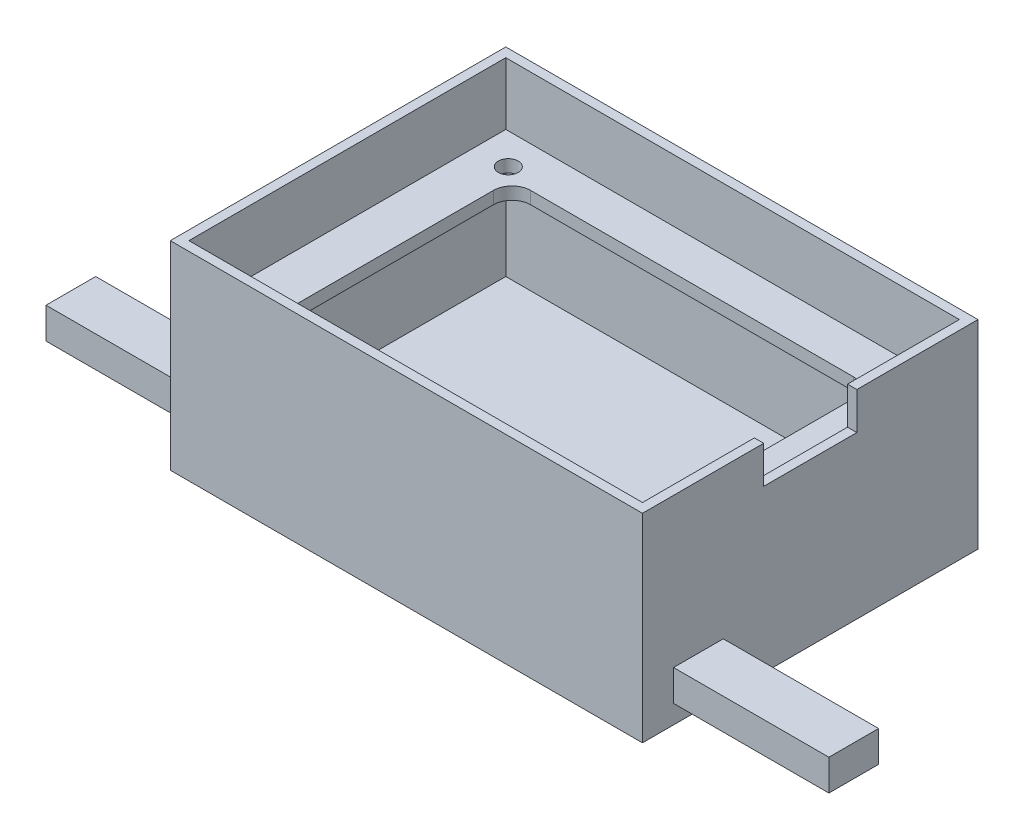
SolidWorks part; units mm, degrees
ref_plane "Front Plane" through (0, 0, 0) normal (0, 0, 1) x (1, 0, 0)
ref_plane "Top Plane" through (0, 0, 0) normal (0, 1, 0) x (1, 0, 0)
ref_plane "Right Plane" through (0, 0, 0) normal (1, 0, 0) x (0, 0, -1)
sketch "Enclosure Shell Sketch" plane through (0, 0, 0) normal (0, 1, 0) x (1, 0, 0)
  line L1 (38, 27) -> (-38, 27)
  line L2 (38, 27) -> (38, -27)
  line L3 (38, -27) -> (-38, -27)
  line L4 (-38, 27) -> (-38, -27)
  line L5 (38, 27) -> (-38, -27) construction
  line L6 (38, -27) -> (-38, 27) construction
  point P0 (0, 0)
  dimension "D1" = 76
  dimension "D2" = 54
extrude "Enclosure Shell Feature" add sketch "Enclosure Shell Sketch" along normal blind 32
sketch "Enclosure Gap Sketch" plane through (0, 32, 0) normal (0, 1, 0) x (1, 0, 0)
  line L1 (-36.5, 25.5) -> (36.5, 25.5)
  line L2 (-36.5, 25.5) -> (-36.5, -25.5)
  line L3 (-36.5, -25.5) -> (36.5, -25.5)
  line L4 (36.5, 25.5) -> (36.5, -25.5)
  line L5 (-36.5, 25.5) -> (36.5, -25.5) construction
  line L6 (-36.5, -25.5) -> (36.5, 25.5) construction
  point P0 (0, 0)
  dimension "D1" = 51
  dimension "D2" = 73
extrude "Enclosure Gap Feature" cut sketch "Enclosure Gap Sketch" against normal blind 30
sketch "Camera Cord Hole Sketch" plane through (0, 2, 0) normal (0, 1, 0) x (1, 0, 0)
  line L1 (-27.5, -3.5) -> (-7.5, -3.5)
  line L2 (-27.5, -3.5) -> (-27.5, -15.5)
  line L3 (-27.5, -15.5) -> (-7.5, -15.5)
  line L4 (-7.5, -3.5) -> (-7.5, -15.5)
  line L5 (-27.5, -3.5) -> (-7.5, -15.5) construction
  line L6 (-27.5, -15.5) -> (-7.5, -3.5) construction
  line L10 (-36.5, 25.5) -> (-36.5, -25.5) construction
  line L11 (-36.5, -25.5) -> (36.5, -25.5) construction
  point P0 (-17.5, -9.5)
  dimension "D1" = 12
  dimension "D2" = 20
  dimension "D3" = 19
  dimension "D4" = 10
extrude "Camera Cord Hole" cut sketch "Camera Cord Hole Sketch" against normal through all
sketch "Battery Cut Sketch" plane through (38, 0, 0) normal (-1, 0, 0) x (0, 0, 1)
  line L0 (0, 32) -> (7.4925, 32)
  line L1 (-27, 32) -> (27, 32) construction
  line L2 (7.4925, 32) -> (7.4925, 26)
  line L3 (7.4925, 26) -> (-7.5, 26)
  line L4 (-7.5, 26) -> (-7.5, 32)
  line L5 (-7.5, 32) -> (0, 32)
  dimension "D1" = 6
  dimension "D2" = 6
extrude "Battery Cut" cut sketch "Battery Cut Sketch" along normal up to next and the other way through all
sketch "Right Tab Feature Sketch" plane through (38, 0, 0) normal (1, 0, 0) x (0, 0, -1)
  line L1 (-22, 8) -> (-14, 8)
  line L2 (-22, 8) -> (-22, 3)
  line L3 (-22, 3) -> (-14, 3)
  line L4 (-14, 8) -> (-14, 3)
  line L5 (-22, 8) -> (-14, 3) construction
  line L6 (-22, 3) -> (-14, 8) construction
  point P0 (-18, 5.5)
  dimension "D1" = 8
extrude "Right Tab Feature" add sketch "Right Tab Feature Sketch" along normal blind 25
sketch "Left Tab Feature Sketch" plane through (-38, 0, 0) normal (-1, 0, 0) x (0, 0, 1)
  line L1 (14, 8) -> (22, 8)
  line L2 (14, 8) -> (14, 3)
  line L3 (14, 3) -> (22, 3)
  line L4 (22, 8) -> (22, 3)
  line L5 (14, 8) -> (22, 3) construction
  line L6 (14, 3) -> (22, 8) construction
  point P0 (18, 5.5)
  dimension "D1" = 8
  dimension "D2" = 5
extrude "Left Tab Feature" add sketch "Left Tab Feature Sketch" along normal blind 25
sketch "Sketch1" plane through (0, 2, 0) normal (0, 1, 0) x (1, 0, 0)
  line L1 (-38, 27) -> (38, 27)
  line L2 (-38, 27) -> (-38, -27)
  line L3 (-38, -27) -> (38, -27)
  line L4 (38, 27) -> (38, -27)
  line L5 (-38, 27) -> (38, -27) construction
  line L6 (-38, -27) -> (38, 27) construction
  point P0 (0, 0)
extrude "Boss-Extrude1" add sketch "Sketch1" along normal blind 20
sketch "Sketch5" plane through (0, 0, 0) normal (0, -1, 0) x (-1, 0, 0)
  line L1 (36, -25) -> (-36, -25)
  line L2 (36, -25) -> (36, 25)
  line L3 (36, 25) -> (-36, 25)
  line L4 (-36, -25) -> (-36, 25)
  line L5 (36, -25) -> (-36, 25) construction
  line L6 (36, 25) -> (-36, -25) construction
  point P0 (0, 0)
  dimension "D1" = 50
  dimension "D2" = 72
extrude "Cut-Extrude2" cut sketch "Sketch5" against normal blind 18 from offset 2 offset against normal yes
sketch "Screw Shell Sketch" plane through (0, 22, 0) normal (0, 1, 0) x (1, 0, 0)
  line L0 (38, -27) -> (38, -7.4925) construction
  line L1 (-38, 27) -> (-38, -27) construction
  line L3 (-38, -27) -> (38, -27) construction
  line L6 (38, 27) -> (-38, 27) construction
  circle A0 centre (-30.0882, 20.5159) radius 2.5
  circle A1 centre (-32.1, -21.5) radius 2.5
  circle A2 centre (32.1, 21.5) radius 2.5
  circle A3 centre (30.0882, -20.5159) radius 2.5
  dimension "D1" = 62.196
  dimension "D3" = 5.9
  dimension "D5" = 5.9
  dimension "D2" = 5.5
  dimension "D4" = 62.196
  dimension "D6" = 5.5
extrude "Screw Shell Feature" add sketch "Screw Shell Sketch" against normal blind 1
sketch "Screw Hole Sketch" plane through (0, 22, 0) normal (0, 1, 0) x (1, 0, 0)
  line L0 (38, 27) -> (-38, 27) construction
  circle A0 centre (-31.096, 20.5) radius 1.6
  circle A1 centre (-31.1, -20.5) radius 1.6
  circle A2 centre (31.096, -20.5) radius 1.6
  circle A3 centre (31.1, 20.5) radius 1.6
  dimension "D1" = 6.5
sketch "Sketch6" plane through (0, 22, 0) normal (0, 1, 0) x (1, 0, 0)
  line L1 (-29, 19) -> (29, 19)
  line L2 (-29, 19) -> (-29, -19)
  line L3 (-29, -19) -> (29, -19)
  line L4 (29, 19) -> (29, -19)
  line L5 (-29, 19) -> (29, -19) construction
  line L6 (-29, -19) -> (29, 19) construction
  point P0 (0, 0)
  dimension "D1" = 58
  dimension "D2" = 38
extrude "Cut-Extrude3" cut sketch "Sketch6" against normal blind 2
extrude "Cut-Extrude4" cut sketch "Screw Hole Sketch" against normal blind 2
fillet "Fillet1" radius 3 1 edges at (-29, 21, -19)
fillet "Fillet2" radius 3 1 edges at (29, 21, -19)
fillet "Fillet3" radius 3 1 edges at (29, 21, 19)
fillet "Fillet4" radius 3 1 edges at (-29, 21, 19)
